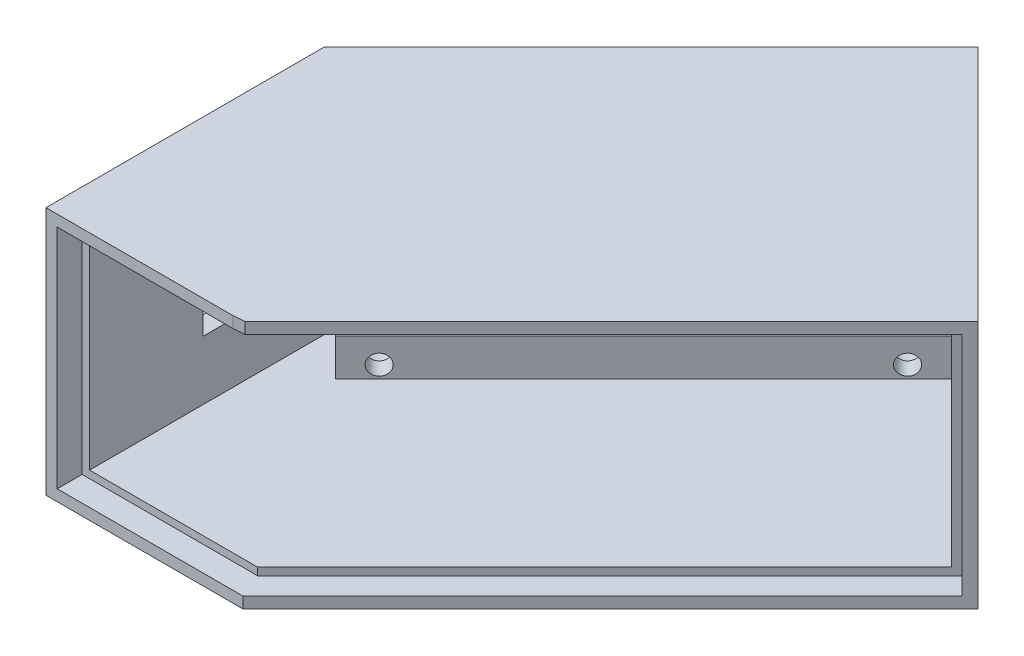
SolidWorks part; units mm, degrees
ref_plane "Спереди" through (0, 0, 0) normal (0, 0, 1) x (1, 0, 0)
ref_plane "Сверху" through (0, 0, 0) normal (0, 1, 0) x (1, 0, 0)
ref_plane "Справа" through (0, 0, 0) normal (1, 0, 0) x (0, 0, -1)
sketch "Sketch1" plane through (0, 0, 0) normal (0, 1, 0) x (1, 0, 0)
  line L0 (-43.3594, -5.3943) -> (-43.3594, 35.3164)
  line L1 (-43.3594, 35.3164) -> (9.115, 87.7907)
  line L2 (9.115, 87.7907) -> (44.4704, 52.4354)
  line L3 (44.4704, 52.4354) -> (-13.3594, -5.3943)
  line L4 (-13.3594, -5.3943) -> (-43.3594, -5.3943)
  dimension "D1" = 74.21
  dimension "D3" = 135
  dimension "D4" = 30
  dimension "D5" = 50
extrude "Boss-Extrude1" add sketch "Sketch1" along normal blind 40
shell "Shell1" thickness 3
sketch "Sketch6" plane through (-3.9825, 0, -3.9825) normal (0.7071, 0, 0.7071) x (0.7071, 0, -0.7071)
  line L0 (-13.2609, 38.2) -> (66.7227, 38.2)
  line L1 (-13.2609, 40) -> (-13.2609, 37) construction
  line L2 (66.7227, 38.2) -> (66.7227, 1.8)
  line L3 (66.7227, 1.8) -> (-13.2609, 1.8)
  line L4 (-13.2609, 3) -> (-13.2609, 0) construction
  line L5 (-13.2609, 40) -> (68.5227, 40) construction
  line L6 (-13.2609, 0) -> (68.5227, 0) construction
  line L7 (68.5227, 40) -> (68.5227, 0) construction
  line L8 (-13.2609, 38.2) -> (-13.2609, 40)
  line L9 (-13.2609, 40) -> (68.5227, 40)
  line L10 (68.5227, 40) -> (68.5227, 0)
  line L11 (68.5227, 0) -> (-13.2609, 0)
  line L12 (-13.2609, 0) -> (-13.2609, 1.8)
  dimension "D1" = 1.8
  dimension "D2" = 1.8
  dimension "D3" = 1.8
extrude "Boss-Extrude2" add sketch "Sketch6" along normal blind 4
sketch "Sketch7" plane through (0, 0, 5.3943) normal (0, 0, 1) x (1, 0, 0)
  line L0 (-13.3594, 1.8) -> (-41.5594, 1.8)
  line L1 (-41.5594, 1.8) -> (-41.5594, 38.2)
  line L2 (-41.5594, 38.2) -> (-13.3594, 38.2)
  line L3 (-43.3594, 40) -> (-43.3594, 0) construction
  line L4 (-13.3594, 38.2) -> (-13.3594, 40)
  line L5 (-13.3594, 40) -> (-43.3594, 40)
  line L6 (-43.3594, 40) -> (-43.3594, 0)
  line L7 (-43.3594, 0) -> (-13.3594, 0)
  line L8 (-13.3594, 0) -> (-13.3594, 1.8)
  dimension "D1" = 1.8
extrude "Boss-Extrude3" add sketch "Sketch7" along normal blind 4
sketch "Sketch8" plane through (0, 0, 0) normal (0, -1, 0) x (1, 0, 0)
  line L0 (-13.3594, 9.3943) -> (-11.7025, 9.3943)
  line L1 (-11.7025, 9.3943) -> (-10.5309, 8.2228)
  line L2 (-10.5309, 8.2228) -> (-13.3594, 5.3943)
  line L3 (-13.3594, 5.3943) -> (-13.3594, 9.3943)
  line L4 (-10.5309, 8.2228) -> (47.2988, -49.607) construction
extrude "Boss-Extrude4" add sketch "Sketch8" against normal up to surface (1.8 mm away) up to face at (16.3333, 1.8, -21.4699)
sketch "Sketch9" plane through (0, 40, 0) normal (0, 1, 0) x (1, 0, 0)
  line L0 (-13.3594, -5.3943) -> (-10.5309, -8.2228)
  line L1 (-10.5309, -8.2228) -> (-11.5537, -9.2455)
  line L2 (-11.5537, -9.2455) -> (-13.3594, -9.3943)
  line L3 (-13.3594, -9.3943) -> (-13.3594, -5.3943)
  line L4 (47.2988, 49.607) -> (-10.5309, -8.2228) construction
extrude "Boss-Extrude5" add sketch "Sketch9" against normal up to surface (1.8 mm away) up to face at (16.3333, 38.2, -21.4699)
sketch "Sketch10" plane through (-37.2165, 0, -37.2165) normal (0.7071, 0, 0.7071) x (0.7071, 0, -0.7071)
  line L0 (65.5227, 20) -> (-4.4446, 20) construction
  line L1 (65.5227, 37) -> (65.5227, 3) construction
  line L2 (-4.4446, 37) -> (-4.4446, 3) construction
  line L3 (60.5227, 35) -> (60.5227, 5) construction
  line L4 (68.5227, 40) -> (68.5227, 0) construction
  line L5 (0.5227, 35) -> (0.5227, 5) construction
  line L6 (60.5227, 35) -> (0.5227, 35) construction
  circle A0 centre (60.5227, 35) radius 1.65
  circle A1 centre (60.5227, 5) radius 1.65
  circle A2 centre (0.5227, 35) radius 1.65
  circle A3 centre (0.5227, 5) radius 1.65
  point P8 (60.5227, 20)
  point P11 (68.5227, 20)
  dimension "D3" = 3.3
  dimension "D1" = 30
  dimension "D2" = 8
  dimension "D4" = 60
extrude "Cut-Extrude6" cut sketch "Sketch10" against normal through all
sketch "Sketch11" plane through (-40.3594, 0, 0) normal (1, 0, 0) x (0, 0, -1)
  line L0 (19.2076, 37) -> (19.2076, 3) construction
  line L1 (34.0737, 37) -> (-5.3943, 37) construction
  line L2 (34.0737, 3) -> (-5.3943, 3) construction
  line L4 (12.8076, 12.5) -> (25.6076, 12.5)
  line L5 (12.8076, 12.5) -> (12.8076, 27.5)
  line L6 (12.8076, 27.5) -> (25.6076, 27.5)
  line L7 (25.6076, 12.5) -> (25.6076, 27.5)
  line L8 (12.8076, 12.5) -> (25.6076, 27.5) construction
  line L9 (12.8076, 27.5) -> (25.6076, 12.5) construction
  point P6 (19.2076, 20)
  dimension "D1" = 15
  dimension "D2" = 12.8
extrude "Cut-Extrude7" cut sketch "Sketch11" against normal up to surface (3 mm away) up to face at (-43.3594, 20, -12.961)
sketch "Sketch12" plane through (-37.2165, 0, -37.2165) normal (0.7071, 0, 0.7071) x (0.7071, 0, -0.7071)
  line L0 (65.5227, 37) -> (-4.4446, 3) construction
  line L1 (-4.4446, 37) -> (-4.4446, 3) construction
  line L3 (65.5227, 3) -> (-4.4446, 3)
  line L4 (65.5227, 3) -> (65.5227, 37)
  line L5 (65.5227, 37) -> (-4.4446, 37)
  line L6 (-4.4446, 3) -> (-4.4446, 37)
  line L7 (65.5227, 3) -> (-4.4446, 37) construction
  line L8 (65.5227, 37) -> (-4.4446, 3) construction
  circle A0 centre (0.5227, 35) radius 1.6
  circle A1 centre (60.5227, 35) radius 1.6
  circle A2 centre (60.5227, 5) radius 1.6
  circle A3 centre (0.5227, 5) radius 1.6
  point P5 (30.539, 20)
extrude "Boss-Extrude7" add sketch "Sketch12" along normal blind 10
sketch "Sketch13" plane through (-39.3379, 0, -39.3379) normal (-0.7071, 0, -0.7071) x (-0.7071, 0, 0.7071)
  circle A0 centre (-0.5227, 35) radius 3.5
  circle A1 centre (-0.5227, 5) radius 3.5
  circle A2 centre (-60.5227, 5) radius 3.5
  circle A3 centre (-60.5227, 35) radius 3.5
  dimension "D1" = 7
extrude "Cut-Extrude9" cut sketch "Sketch13" against normal blind 10
sketch "Sketch14" plane through (-30.1455, 0, -30.1455) normal (0.7071, 0, 0.7071) x (0.7071, 0, -0.7071)
  line L0 (-4.4446, 37) -> (65.5227, 3) construction
  line L1 (-4.4446, 37) -> (-4.4446, 3) construction
  line L2 (65.5227, 9) -> (-4.4446, 9)
  line L3 (65.5227, 9) -> (65.5227, 31)
  line L4 (65.5227, 31) -> (-4.4446, 31)
  line L5 (-4.4446, 9) -> (-4.4446, 31)
  line L6 (65.5227, 9) -> (-4.4446, 31) construction
  line L7 (65.5227, 31) -> (-4.4446, 9) construction
  point P4 (30.539, 20)
  dimension "D1" = 22
extrude "Cut-Extrude10" cut sketch "Sketch14" against normal blind 10
